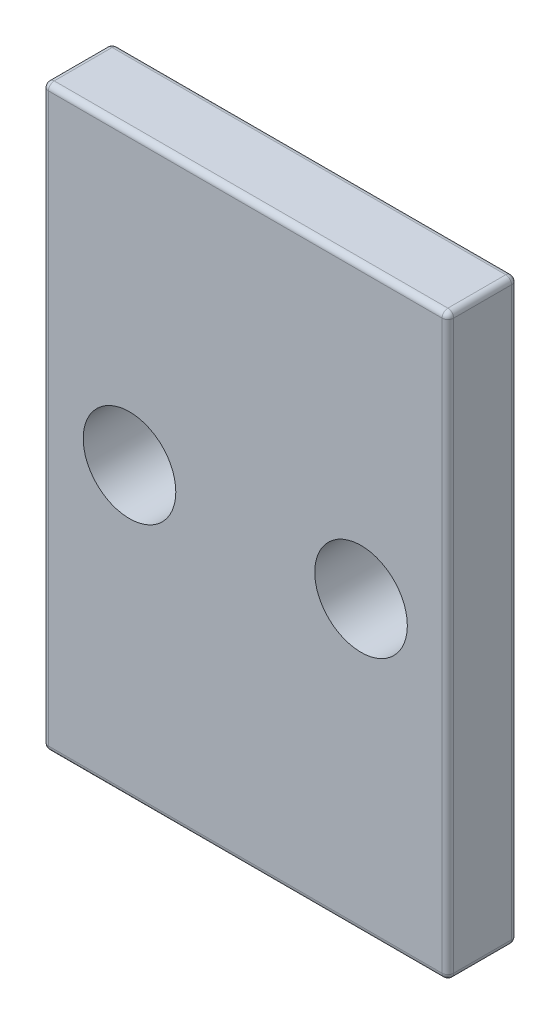
SolidWorks part; units mm, degrees
ref_plane "Płaszczyzna przednia" through (0, 0, 0) normal (0, 0, 1) x (1, 0, 0)
ref_plane "Płaszczyzna górna" through (0, 0, 0) normal (0, 1, 0) x (1, 0, 0)
ref_plane "Płaszczyzna prawa" through (0, 0, 0) normal (1, 0, 0) x (0, 0, -1)
sketch "Sketch1" plane through (0, 0, 0) normal (0, 0, 1) x (1, 0, 0)
  line L0 (0, 0) -> (26.9472, 0) construction
  line L1 (-17.5, 25) -> (17.5, 25)
  line L2 (-17.5, 25) -> (-17.5, -25)
  line L3 (-17.5, -25) -> (17.5, -25)
  line L4 (17.5, 25) -> (17.5, -25)
  line L5 (-17.5, 25) -> (17.5, -25) construction
  line L6 (-17.5, -25) -> (17.5, 25) construction
  line L7 (26.9472, 0) -> (-27.3648, 0) construction
  circle A0 centre (-10, 0) radius 4
  circle A1 centre (10, 0) radius 4
  point P0 (0, 0)
  dimension "D5" = 8
  dimension "D6" = 8
  dimension "D1" = 20
  dimension "D2" = 10
  dimension "D3" = 35
  dimension "D4" = 50
extrude "Boss-Extrude1" add sketch "Sketch1" along normal blind 6
fillet "Fillet1" radius 0.5 12 edges at (0, 25, 6) (0, 25, 0) (17.5, 0, 6) (17.5, 25, 3) (17.5, 0, 0) (0, -25, 6) (17.5, -25, 3) (0, -25, 0) (-17.5, 25, 3) (-17.5, 0, 6) (-17.5, -25, 3) (-17.5, 0, 0)
